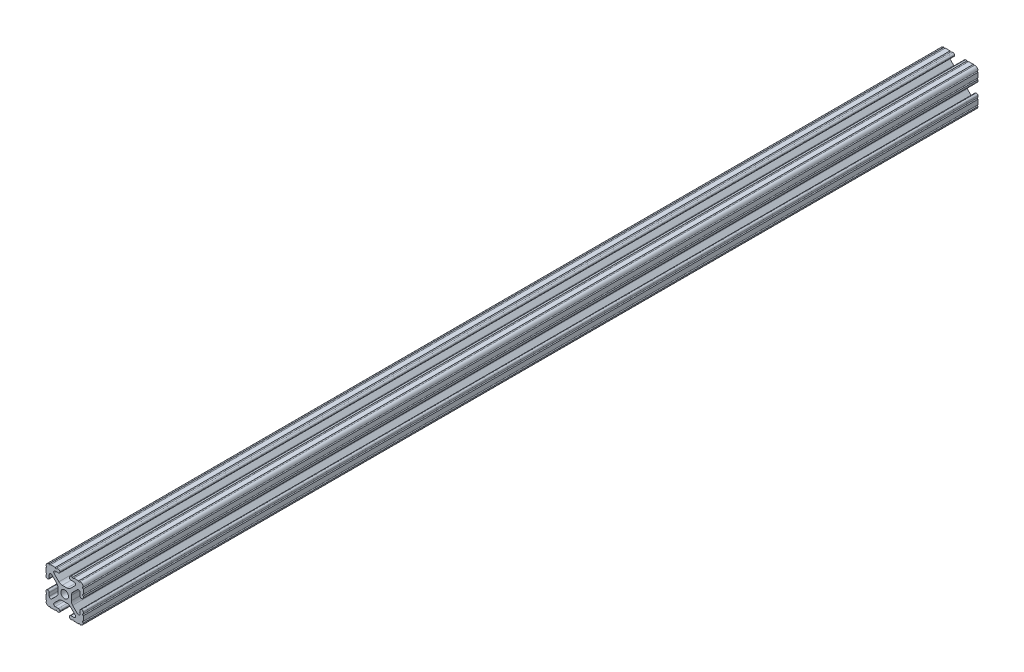
SolidWorks part; units mm, degrees
ref_plane "Front Plane" through (0, 0, 0) normal (0, 0, 1) x (1, 0, 0)
ref_plane "Top Plane" through (0, 0, 0) normal (0, 1, 0) x (1, 0, 0)
ref_plane "Right Plane" through (0, 0, 0) normal (1, 0, 0) x (0, 0, -1)
sketch "Sketch1" plane through (0, 0, 0) normal (0, 0, 1) x (1, 0, 0)
  line L88 (-7.1797, -8.6452) -> (-3.9523, -5.4237)
  line L89 (-1.7093, -4.4958) -> (1.7093, -4.4958)
  line L90 (3.9523, -5.4237) -> (7.1797, -8.6452)
  line L91 (6.4164, -10.4902) -> (4.2875, -10.4902)
  line L92 (3.2385, -11.5392) -> (3.2385, -11.651)
  line L93 (4.2875, -12.7) -> (5.3171, -12.7)
  line L94 (6.3331, -12.7) -> (9.5504, -12.7)
  line L95 (12.7, -9.5504) -> (12.7, -6.3331)
  line L96 (12.7, -5.3171) -> (12.7, -4.2875)
  line L97 (11.651, -3.2385) -> (11.5392, -3.2385)
  line L98 (10.4902, -4.2875) -> (10.4902, -6.4021)
  line L99 (8.7371, -7.1294) -> (5.441, -3.8408)
  line L100 (4.5085, -1.5932) -> (4.5085, 1.5932)
  line L101 (5.441, 3.8408) -> (8.7371, 7.1294)
  line L102 (10.4902, 6.4021) -> (10.4902, 4.2875)
  line L103 (11.5392, 3.2385) -> (11.651, 3.2385)
  line L104 (12.7, 4.2875) -> (12.7, 5.3171)
  line L105 (12.7, 6.3331) -> (12.7, 9.5504)
  line L106 (9.5504, 12.7) -> (6.3331, 12.7)
  line L107 (5.3171, 12.7) -> (4.2875, 12.7)
  line L108 (3.2385, 11.651) -> (3.2385, 11.5392)
  line L109 (4.2875, 10.4902) -> (6.4768, 10.4902)
  line L110 (7.207, 8.7244) -> (3.8983, 5.4232)
  line L111 (1.6558, 4.4958) -> (-1.6558, 4.4958)
  line L112 (-3.8983, 5.4232) -> (-7.207, 8.7244)
  line L113 (-6.4768, 10.4902) -> (-4.2875, 10.4902)
  line L114 (-3.2385, 11.5392) -> (-3.2385, 11.651)
  line L115 (-4.2875, 12.7) -> (-5.3171, 12.7)
  line L116 (-6.3331, 12.7) -> (-9.5504, 12.7)
  line L117 (-12.7, 9.5504) -> (-12.7, 6.3331)
  line L118 (-12.7, 5.3171) -> (-12.7, 4.2875)
  line L119 (-11.651, 3.2385) -> (-11.5392, 3.2385)
  line L120 (-10.4902, 4.2875) -> (-10.4902, 6.4021)
  line L121 (-8.7371, 7.1294) -> (-5.441, 3.8408)
  line L122 (-4.5085, 1.5932) -> (-4.5085, -1.5932)
  line L123 (-5.441, -3.8408) -> (-8.7371, -7.1294)
  line L124 (-10.4902, -6.4021) -> (-10.4902, -4.2875)
  line L125 (-11.5392, -3.2385) -> (-11.651, -3.2385)
  line L126 (-12.7, -4.2875) -> (-12.7, -5.3171)
  line L127 (-12.7, -6.3331) -> (-12.7, -9.5504)
  line L128 (-9.5504, -12.7) -> (-6.3331, -12.7)
  line L129 (-5.3171, -12.7) -> (-4.2875, -12.7)
  line L130 (-3.2385, -11.651) -> (-3.2385, -11.5392)
  line L131 (-4.2875, -10.4902) -> (-6.4164, -10.4902)
  circle A1 centre (0, 0) radius 2.6035
  arc A104 (-7.1797, -8.6452) -> (-6.4164, -10.4902) centre (-6.4164, -9.4098) ccw
  arc A105 (-1.7093, -4.4958) -> (-3.9523, -5.4237) centre (-1.7093, -7.6708) ccw
  arc A106 (3.9523, -5.4237) -> (1.7093, -4.4958) centre (1.7093, -7.6708) ccw
  arc A107 (6.4164, -10.4902) -> (7.1797, -8.6452) centre (6.4164, -9.4098) ccw
  arc A108 (4.2875, -10.4902) -> (3.2385, -11.5392) centre (4.2875, -11.5392) ccw
  arc A109 (3.2385, -11.651) -> (4.2875, -12.7) centre (4.2875, -11.651) ccw
  arc A110 (6.3331, -12.7) -> (5.3171, -12.7) centre (5.8251, -12.7) ccw
  arc A111 (10.5664, -12.6998) -> (9.5504, -12.7) centre (10.0584, -12.7) ccw
  arc A112 (10.5664, -12.6998) -> (12.6998, -10.5664) centre (10.5918, -10.5918) ccw
  arc A113 (12.7, -9.5504) -> (12.6998, -10.5664) centre (12.7, -10.0584) ccw
  arc A114 (12.7, -5.3171) -> (12.7, -6.3331) centre (12.7, -5.8251) ccw
  arc A115 (12.7, -4.2875) -> (11.651, -3.2385) centre (11.651, -4.2875) ccw
  arc A116 (11.5392, -3.2385) -> (10.4902, -4.2875) centre (11.5392, -4.2875) ccw
  arc A117 (8.7371, -7.1294) -> (10.4902, -6.4021) centre (9.4628, -6.4021) ccw
  arc A118 (4.5085, -1.5932) -> (5.441, -3.8408) centre (7.6835, -1.5932) ccw
  arc A119 (5.441, 3.8408) -> (4.5085, 1.5932) centre (7.6835, 1.5932) ccw
  arc A120 (10.4902, 6.4021) -> (8.7371, 7.1294) centre (9.4628, 6.4021) ccw
  arc A121 (10.4902, 4.2875) -> (11.5392, 3.2385) centre (11.5392, 4.2875) ccw
  arc A122 (11.651, 3.2385) -> (12.7, 4.2875) centre (11.651, 4.2875) ccw
  arc A123 (12.7, 6.3331) -> (12.7, 5.3171) centre (12.7, 5.8251) ccw
  arc A124 (12.6998, 10.5664) -> (12.7, 9.5504) centre (12.7, 10.0584) ccw
  arc A125 (12.6998, 10.5664) -> (10.5664, 12.6998) centre (10.5918, 10.5918) ccw
  arc A126 (9.5504, 12.7) -> (10.5664, 12.6998) centre (10.0584, 12.7) ccw
  arc A127 (5.3171, 12.7) -> (6.3331, 12.7) centre (5.8251, 12.7) ccw
  arc A128 (4.2875, 12.7) -> (3.2385, 11.651) centre (4.2875, 11.651) ccw
  arc A129 (3.2385, 11.5392) -> (4.2875, 10.4902) centre (4.2875, 11.5392) ccw
  arc A130 (7.207, 8.7244) -> (6.4768, 10.4902) centre (6.4768, 9.4563) ccw
  arc A131 (1.6558, 4.4958) -> (3.8983, 5.4232) centre (1.6558, 7.6708) ccw
  arc A132 (-3.8983, 5.4232) -> (-1.6558, 4.4958) centre (-1.6558, 7.6708) ccw
  arc A133 (-6.4768, 10.4902) -> (-7.207, 8.7244) centre (-6.4768, 9.4563) ccw
  arc A134 (-4.2875, 10.4902) -> (-3.2385, 11.5392) centre (-4.2875, 11.5392) ccw
  arc A135 (-3.2385, 11.651) -> (-4.2875, 12.7) centre (-4.2875, 11.651) ccw
  arc A136 (-6.3331, 12.7) -> (-5.3171, 12.7) centre (-5.8251, 12.7) ccw
  arc A137 (-10.5664, 12.6998) -> (-9.5504, 12.7) centre (-10.0584, 12.7) ccw
  arc A138 (-10.5664, 12.6998) -> (-12.6998, 10.5664) centre (-10.5918, 10.5918) ccw
  arc A139 (-12.7, 9.5504) -> (-12.6998, 10.5664) centre (-12.7, 10.0584) ccw
  arc A140 (-12.7, 5.3171) -> (-12.7, 6.3331) centre (-12.7, 5.8251) ccw
  arc A141 (-12.7, 4.2875) -> (-11.651, 3.2385) centre (-11.651, 4.2875) ccw
  arc A142 (-11.5392, 3.2385) -> (-10.4902, 4.2875) centre (-11.5392, 4.2875) ccw
  arc A143 (-8.7371, 7.1294) -> (-10.4902, 6.4021) centre (-9.4628, 6.4021) ccw
  arc A144 (-4.5085, 1.5932) -> (-5.441, 3.8408) centre (-7.6835, 1.5932) ccw
  arc A145 (-5.441, -3.8408) -> (-4.5085, -1.5932) centre (-7.6835, -1.5932) ccw
  arc A146 (-10.4902, -6.4021) -> (-8.7371, -7.1294) centre (-9.4628, -6.4021) ccw
  arc A147 (-10.4902, -4.2875) -> (-11.5392, -3.2385) centre (-11.5392, -4.2875) ccw
  arc A148 (-11.651, -3.2385) -> (-12.7, -4.2875) centre (-11.651, -4.2875) ccw
  arc A149 (-12.7, -6.3331) -> (-12.7, -5.3171) centre (-12.7, -5.8251) ccw
  arc A150 (-12.6998, -10.5664) -> (-12.7, -9.5504) centre (-12.7, -10.0584) ccw
  arc A151 (-12.6998, -10.5664) -> (-10.5664, -12.6998) centre (-10.5918, -10.5918) ccw
  arc A152 (-9.5504, -12.7) -> (-10.5664, -12.6998) centre (-10.0584, -12.7) ccw
  arc A153 (-5.3171, -12.7) -> (-6.3331, -12.7) centre (-5.8251, -12.7) ccw
  arc A154 (-4.2875, -12.7) -> (-3.2385, -11.651) centre (-4.2875, -11.651) ccw
  arc A155 (-3.2385, -11.5392) -> (-4.2875, -10.4902) centre (-4.2875, -11.5392) ccw
extrude "Boss-Extrude1" add sketch "Sketch1" along normal mid plane 787.4
sketch "Sketch3" plane through (0, 0, 393.7) normal (0, 0, 1) x (1, 0, 0)
  line L1 (-19.2273, 18.2006) -> (19.2273, 18.2006)
  line L2 (-19.2273, 18.2006) -> (-19.2273, -18.2006)
  line L3 (-19.2273, -18.2006) -> (19.2273, -18.2006)
  line L4 (19.2273, 18.2006) -> (19.2273, -18.2006)
  line L5 (-19.2273, 18.2006) -> (19.2273, -18.2006) construction
  line L6 (-19.2273, -18.2006) -> (19.2273, 18.2006) construction
  point P0 (0, 0)
extrude "Cut-Extrude2" cut sketch "Sketch3" against normal blind 177.8
sketch "Sketch4" plane through (4.5085, 0, 0) normal (1, 0, 0) x (0, 0, -1)
  line L0 (393.7, -1.5932) -> (393.7, 1.5932) construction
  line L1 (-215.9, 12.6998) -> (393.7, 12.6998) construction
  line L3 (-215.9, -1.5932) -> (-215.9, 1.5932) construction
  circle A0 centre (374.65, -0.0002) radius 3.18
  circle A1 centre (-196.85, -0.0002) radius 3.18
  point P8 (-188.5243, -1.5932)
  dimension "D2" = 6.36
  dimension "D4" = 6.36
  dimension "D1" = 19.05
  dimension "D3" = 12.7
  dimension "D5" = 19.05
  dimension "D6" = 12.7
extrude "Cut-Extrude3" cut sketch "Sketch4" against normal through all both and the other way through all
